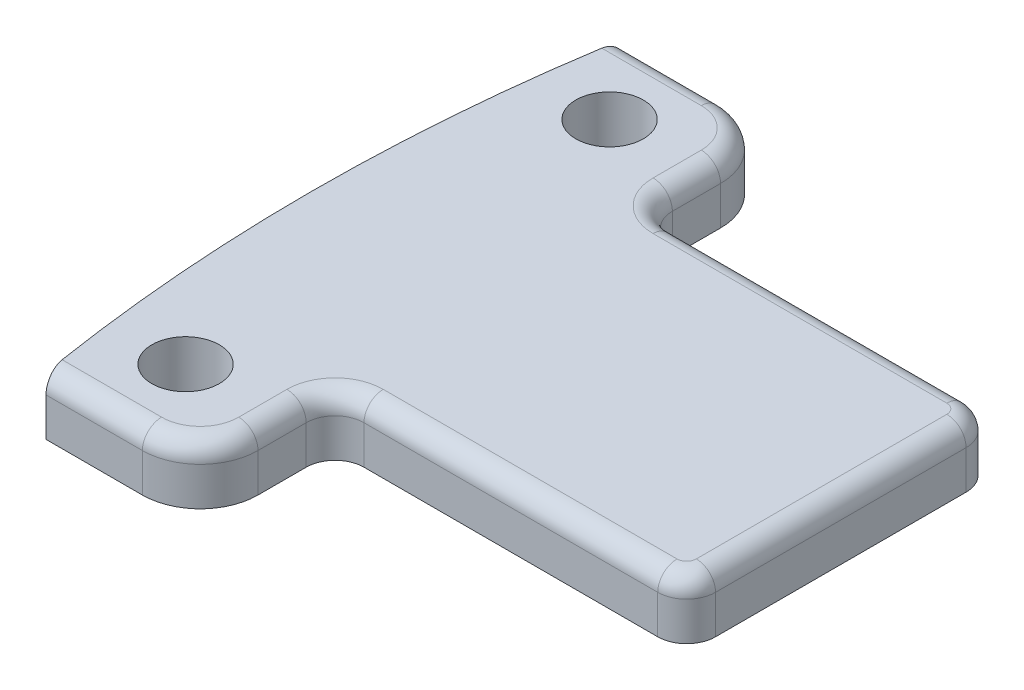
SolidWorks part; units mm, degrees
ref_plane "Front Plane" through (0, 0, 0) normal (0, 0, 1) x (1, 0, 0)
ref_plane "Top Plane" through (0, 0, 0) normal (0, 1, 0) x (1, 0, 0)
ref_plane "Right Plane" through (0, 0, 0) normal (1, 0, 0) x (0, 0, -1)
sketch "Sketch1" plane through (0, 0, 0) normal (0, 1, 0) x (1, 0, 0)
  line L0 (-13.75, 0) -> (13.75, 0) construction
  line L1 (-12.4912, 15) -> (-4.4912, 15)
  line L3 (-12.4912, -15) -> (-4.4912, -15)
  line L4 (13.75, 8) -> (13.75, -8)
  line L5 (-4.4912, 15) -> (-4.4912, 8)
  line L6 (-4.4912, 8) -> (13.75, 8)
  line L7 (13.75, -8) -> (-4.4912, -8)
  line L8 (-4.4912, -8) -> (-4.4912, -15)
  arc A0 (-12.4912, 15) -> (-12.4912, -15) centre (76.25, 0) ccw
  dimension "D5" = 90
  dimension "D1" = 27.5
  dimension "D2" = 30
  dimension "D3" = 8
  dimension "D4" = 16
extrude "Boss-Extrude1" add sketch "Sketch1" along normal blind 3
sketch "Sketch2" plane through (0, 3, 0) normal (0, 1, 0) x (1, 0, 0)
  line L0 (13.75, -8) -> (13.75, 8) construction
  circle A0 centre (-9.25, 11) radius 1.75
  dimension "D3" = 3.5
  dimension "D1" = 11
  dimension "D2" = 23
extrude "Cut-Extrude1" cut sketch "Sketch2" against normal through all
mirror "Mirror1" about plane through (0, 0, 0) normal (0, 0, 1) of "Cut-Extrude1"
fillet "Fillet1" radius 1.5 4 edges at (-4.4912, 1.5, -8) (-4.4912, 1.5, 8) (13.75, 1.5, -8) (13.75, 1.5, 8)
fillet "Fillet3" radius 3 2 edges at (-4.4912, 1.5, -15) (-4.4912, 1.5, 15)
fillet "Fillet2" radius 1 13 edges at (-9.9912, 3, 15) (-4.4912, 3, 10.75) (-4.0519, 3, 8.4393) (-9.9912, 3, -15) (-4.4912, 3, -10.75) (-4.0519, 3, -8.4393) (4.6294, 3, -8) (13.3107, 3, -7.5607) (13.75, 3, 0) (13.3107, 3, 7.5607) (4.6294, 3, 8) (-5.3699, 3, 14.1213) (-5.3699, 3, -14.1213)
